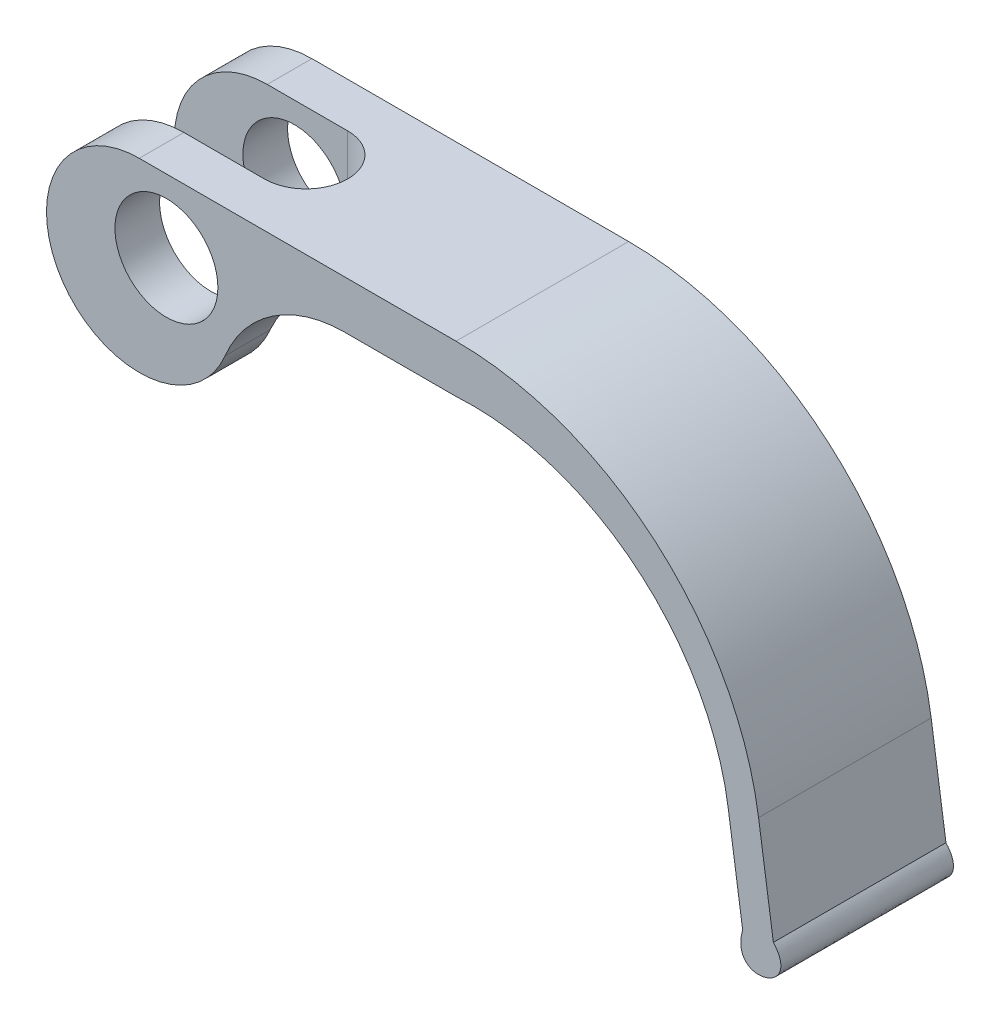
SolidWorks part; units mm, degrees
material "1060 Alloy"
ref_plane "Front Plane" through (0, 0, 0) normal (0, 0, 1) x (1, 0, 0)
ref_plane "Top Plane" through (0, 0, 0) normal (0, 1, 0) x (1, 0, 0)
ref_plane "Right Plane" through (0, 0, 0) normal (1, 0, 0) x (0, 0, -1)
sketch "Sketch1" plane through (0, 0, 0) normal (0, 0, 1) x (1, 0, 0)
  line L0 (-2.1748, 5.8293) -> (23.2252, 5.8293)
  line L1 (-9.4401, 0) -> (6.8176, 0) construction
  line L2 (48.6751, -23.2029) -> (47.4892, -15.1305)
  line L3 (14.3234, 1.9873) -> (23.2252, 1.9873)
  line L4 (46.2123, -23.5647) -> (45.0559, -15.6925)
  circle A0 centre (0, 0) radius 4.1275
  arc A1 (-2.1748, 5.8293) -> (4.7054, -4.4502) centre (-2.1748, -1.6129) ccw
  arc A2 (47.4892, -15.1305) -> (23.2252, 5.8293) centre (23.2252, -18.6951) ccw
  arc A4 (4.7054, -4.4502) -> (14.3234, 1.9873) centre (14.3234, -8.4166) cw
  arc A5 (45.0559, -15.6925) -> (23.2252, 1.9873) centre (24.5407, -18.7063) ccw
  spline S0 degree 3 poles (46.2123, -23.5647) (45.0569, -27.6818) (51.1702, -26.0068) (48.6751, -23.2029) knots 0 0 0 0 1 1 1 1
  point P5 (0, 4.1275)
  point P8 (0, -4.1275)
  point P9 (48.6751, -23.2029)
  point P17 (-2.1748, -9.0551)
  dimension "D1" = 8.255
  dimension "D2" = 1.7018
  dimension "D8" = 7.4422
  dimension "D3" = 4.9276
  dimension "D4" = 25.4
  dimension "D5" = 58.1152
  dimension "D6" = 29.0322
  dimension "D7" = 2.4892
  dimension "D9" = 8.9018
extrude "Boss-Extrude1" add sketch "Sketch1" along normal blind 13.843
sketch "Sketch2" plane through (0, 5.8293, 0) normal (0, 1, 0) x (1, 0, 0)
  line L0 (-9.617, 0) -> (-9.617, -13.843) construction
  line L1 (4.2768, -3.5814) -> (-9.617, -3.5814)
  line L3 (4.2768, -10.2616) -> (-9.617, -10.2616)
  line L6 (23.2252, -13.843) -> (-2.1748, -13.843) construction
  line L7 (23.2252, 0) -> (-2.1748, 0) construction
  line L8 (-9.617, -3.5814) -> (-9.617, -10.2616)
  arc A0 (4.2768, -10.2616) -> (4.2768, -3.5814) centre (4.2768, -6.9215) ccw
  dimension "D3" = 3.3401
  dimension "D1" = 13.8938
  dimension "D2" = 3.5814
  dimension "D4" = 3.5814
extrude "Cut-Extrude1" cut sketch "Sketch2" against normal blind 21.463
